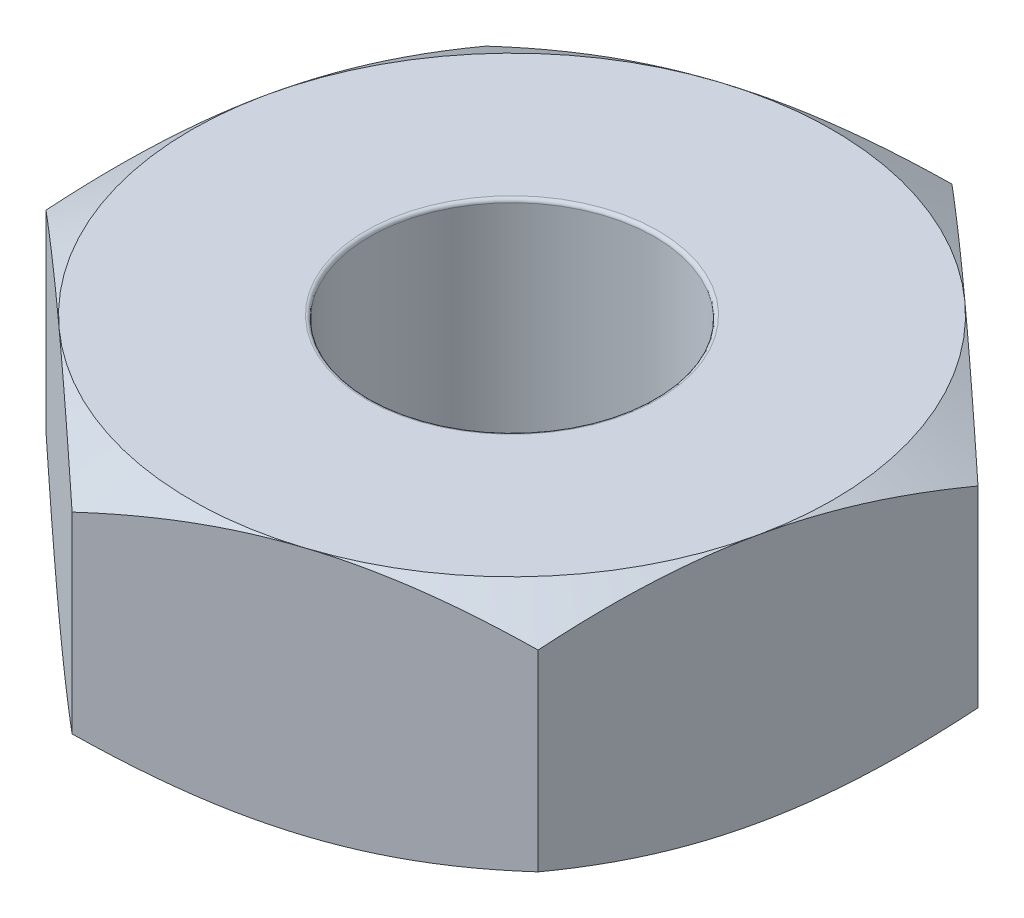
SolidWorks part; units mm, degrees
ref_plane "Front Plane" through (0, 0, 0) normal (0, 0, 1) x (1, 0, 0)
ref_plane "Top Plane" through (0, 0, 0) normal (0, 1, 0) x (1, 0, 0)
ref_plane "Right Plane" through (0, 0, 0) normal (1, 0, 0) x (0, 0, -1)
sketch "Sketch1" plane through (0, 0, 0) normal (0, 1, 0) x (1, 0, 0)
  line L1 (-2.4729, -0.7966) -> (-0.5466, -2.5399)
  line L2 (-0.5466, -2.5399) -> (1.9264, -1.7433)
  line L3 (1.9264, -1.7433) -> (2.4729, 0.7966)
  line L4 (2.4729, 0.7966) -> (0.5466, 2.5399)
  line L5 (0.5466, 2.5399) -> (-1.9264, 1.7433)
  line L6 (-1.9264, 1.7433) -> (-2.4729, -0.7966)
  circle A0 centre (0, 0) radius 1
  circle A1 centre (0, 0) radius 2.25 construction
  dimension "D1" = 2
  dimension "D2" = 4.5
extrude "Boss-Extrude1" add sketch "Sketch1" along normal blind 1.75
sketch "Sketch2" plane through (0, 1.75, 0) normal (0, 1, 0) x (1, 0, 0)
  circle A0 centre (0, 0) radius 2.25 construction
  circle A1 centre (0, 0) radius 2.25
extrude "Cut-Extrude1" cut sketch "Sketch2" against normal blind 1.75 draft 60 flip side to cut
sketch "Sketch3" plane through (0, 0, 0) normal (0, -1, 0) x (1, 0, 0)
  circle A0 centre (0, 0) radius 2.25 construction
  circle A1 centre (0, 0) radius 2.25
extrude "Cut-Extrude2" cut sketch "Sketch3" against normal blind 1.75 draft 60 flip side to cut
fillet "Fillet1" radius 0.025 2 edges at (0, 0, 1) (0, 1.75, 1)
